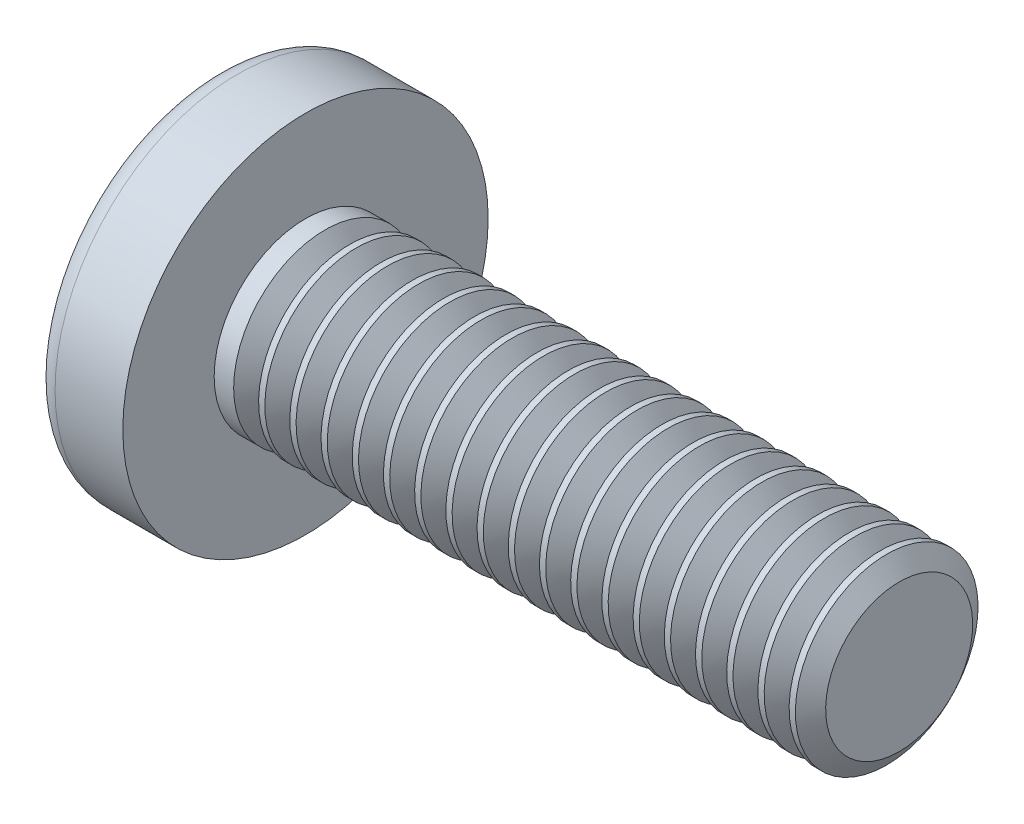
SolidWorks part; units mm, degrees
ref_plane "Plane1" through (0, 0, 0) normal (0, 0, 1) x (1, 0, 0)
ref_plane "Plane2" through (0, 0, 0) normal (0, 1, 0) x (1, 0, 0)
ref_plane "Plane3" through (0, 0, 0) normal (1, 0, 0) x (0, 0, -1)
sketch "BodySke" plane through (0, 0, 0) normal (0, 0, 1) x (1, 0, 0)
  line L0 (3.1, 2) -> (3.1, 4)
  line L1 (3.8, 6.35) -> (3.8, -3.175) construction
  line L2 (-25.4, 0) -> (127, 0) construction
  line L3 (16.1, 0) -> (0, 0)
  line L4 (3.1, 2) -> (16.1, 2)
  line L5 (16.1, 2) -> (16.1, 0)
  line L6 (1.6164, 4) -> (3.1, 4)
  line L7 (3.1, -2) -> (16.1, -2) construction
  line L8 (3.1, 6.35) -> (3.1, -3.175) construction
  arc A0 (1.227, 3.8007) -> (0, 0) centre (6.5, 0) ccw
  arc A2 (1.227, 3.8007) -> (1.6164, 4) centre (1.6164, 3.52) cw
  dimension "Head_crown_rad" = 6.5
  dimension "Head_fillet_rad" = 0.48
  dimension "Diameter" = 4
  dimension "Length" = 13
  dimension "Head_ht" = 3.1
  dimension "Head_dia" = 8
  dimension "Advance" = 0.7
  dimension "Thread_nom" = 13
revolve "Base-Revolve" add sketch "BodySke" angle 360 about L2
cosmetic thread "ThreadCosmetic" [suppressed] parameters "Thread_length"=12.3, "Thread_minor"=3.22
sketch "Sketch3" plane through (0, 0, 0) normal (1, 0, 0) x (0, 0, -1)
  line L0 (0.465, -2.2) -> (-0.465, -2.2)
  line L1 (0.465, -2.2) -> (0.465, 2.2)
  line L2 (-0.465, 2.2) -> (0.465, 2.2)
  line L3 (-0.465, 2.2) -> (-0.465, -2.2)
  dimension "Cross_dia" = 4.4
  dimension "D1" = 2.2
  dimension "Cross_width" = 0.93
  dimension "D2" = 0.465
ref_plane "Plane4" through (2.45, 0, 0) normal (1, 0, 0) x (0, 0, -1)
sketch "Sketch4" plane through (2.45, 0, 0) normal (1, 0, 0) x (0, 0, -1)
  line L0 (0.2325, -0.2325) -> (-0.2325, -0.2325)
  line L1 (0.2325, -0.2325) -> (0.2325, 0.2325)
  line L2 (-0.2325, 0.2325) -> (0.2325, 0.2325)
  line L3 (-0.2325, 0.2325) -> (-0.2325, -0.2325)
  dimension "D2" = 0.465
  dimension "D1" = 0.465
  dimension "D3" = 0.2325
  dimension "D4" = 0.2325
loft "Cut-Loft1" cut profiles "Sketch3", "Sketch4"
pattern_circular "CirPattern1" count 2 every 90 about axis through (0, 0, 0) along (1, 0, 0) of "Cut-Loft1"
sketch "ThdSchSke" plane through (0, 0, 0) normal (0, 0, 1) x (1, 0, 0)
  line L0 (3.8, -1.61) -> (3.5269, -2)
  line L1 (3.8, -1.61) -> (4.0731, -2)
  line L2 (4.0731, -2) -> (4.0731, -2.5)
  line L3 (-3.175, 0) -> (5.1513, 0) construction
  line L5 (4.0731, -2.5) -> (3.5269, -2.5)
  line L6 (3.5269, -2.5) -> (3.5269, -2)
  dimension "Diameter" = 4
  dimension "SideAngle" = 55
  dimension "VeeAngle" = 70
  dimension "Thread_minor" = 3.22
  dimension "Overcut" = 5
  dimension "Start" = 3.8
revolve "ThreadSchematic" cut sketch "ThdSchSke" angle 360 about L3
pattern_linear "ThdSchPat" count 19 spacing 0.6833 along (1, 0, 0) of "ThreadSchematic"
scale "Escala1" scale about centroid uniform scaling yes scale factor 7
equation "\"D1@Sketch3\" = \"Cross_dia@Sketch3\" / 2"
equation "\"D2@Sketch3\" = \"Cross_width@Sketch3\" / 2"
equation "\"D1@Sketch4\" = \"Cross_width@Sketch3\" *.5"
equation "\"D2@Sketch4\" = \"D1@Sketch4\""
equation "\"D3@Sketch4\" = \"D1@Sketch4\" / 2"
equation "\"D4@Sketch4\" = \"D2@Sketch4\" / 2"
equation "\"Thread_length@ThreadCosmetic\" = ((sgn( (\"Length@BodySke\" - \"Advance@BodySke\" ) - \"Thread_nom@BodySke\" )-1)*( (\"Length@BodySke\" - \"Advance@BodySke\" ) - \"Thread_nom@BodySke\" ))/-2+ \"Thread_nom@BodySke\""
equation "\"Thread_minor@ThdSchSke\" = \"Thread_minor@ThreadCosmetic\""
equation "\"Diameter@ThdSchSke\" = \"Diameter@BodySke\""
equation "\"Overcut@ThdSchSke\" = \"Diameter@BodySke\" * 1.25"
equation "\"Start@ThdSchSke\" = \"Head_ht@BodySke\" + \"Length@BodySke\" - \"Thread_length@ThreadCosmetic\"  '---Non-countersunk---"
equation "\"Num_threads@ThdSchPat\" = int( \"Thread_length@ThreadCosmetic\" / \"Advance@BodySke\" + 0.999 )  + 1"
equation "\"Advance@ThdSchPat\" = \"Thread_length@ThreadCosmetic\" /  (\"Num_threads@ThdSchPat\" - 1) 'relax it"
